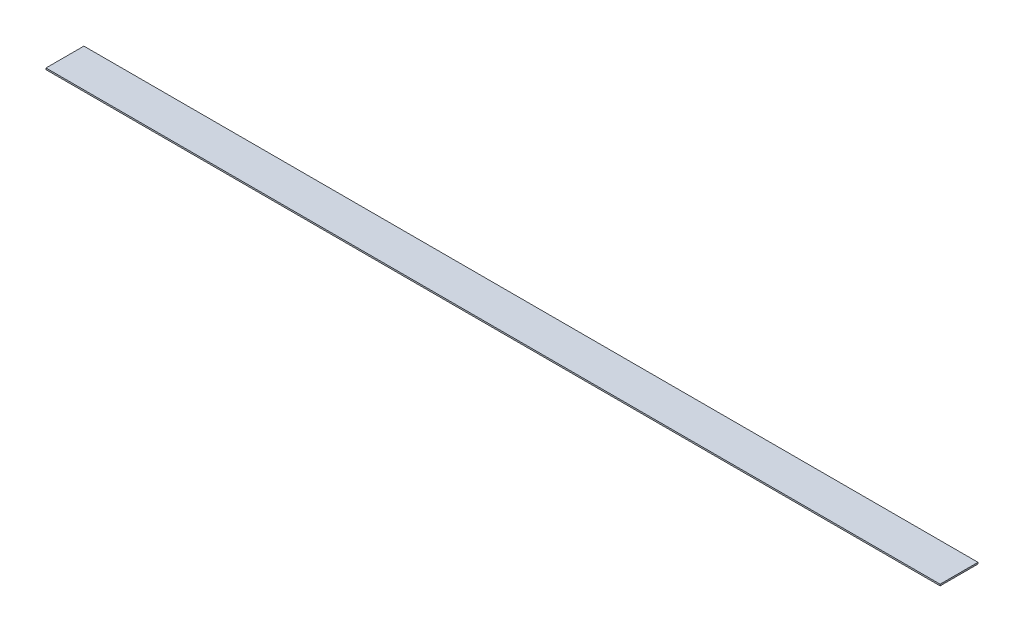
SolidWorks part; units mm, degrees
material "1023 Carbon Steel Sheet (SS)"
ref_plane "Front Plane" through (0, 0, 0) normal (0, 0, 1) x (1, 0, 0)
ref_plane "Top Plane" through (0, 0, 0) normal (0, 1, 0) x (1, 0, 0)
ref_plane "Right Plane" through (0, 0, 0) normal (1, 0, 0) x (0, 0, -1)
sketch "Sketch1" plane through (0, 0, 0) normal (0, 1, 0) x (1, 0, 0)
  line L1 (-295, 12.5) -> (295, 12.5)
  line L2 (-295, 12.5) -> (-295, -12.5)
  line L3 (-295, -12.5) -> (295, -12.5)
  line L4 (295, 12.5) -> (295, -12.5)
  line L5 (-295, 12.5) -> (295, -12.5) construction
  line L6 (-295, -12.5) -> (295, 12.5) construction
  point P0 (0, 0)
  dimension "D1" = 590
  dimension "D2" = 25
extrude "Boss-Extrude1" add sketch "Sketch1" along normal blind 1
